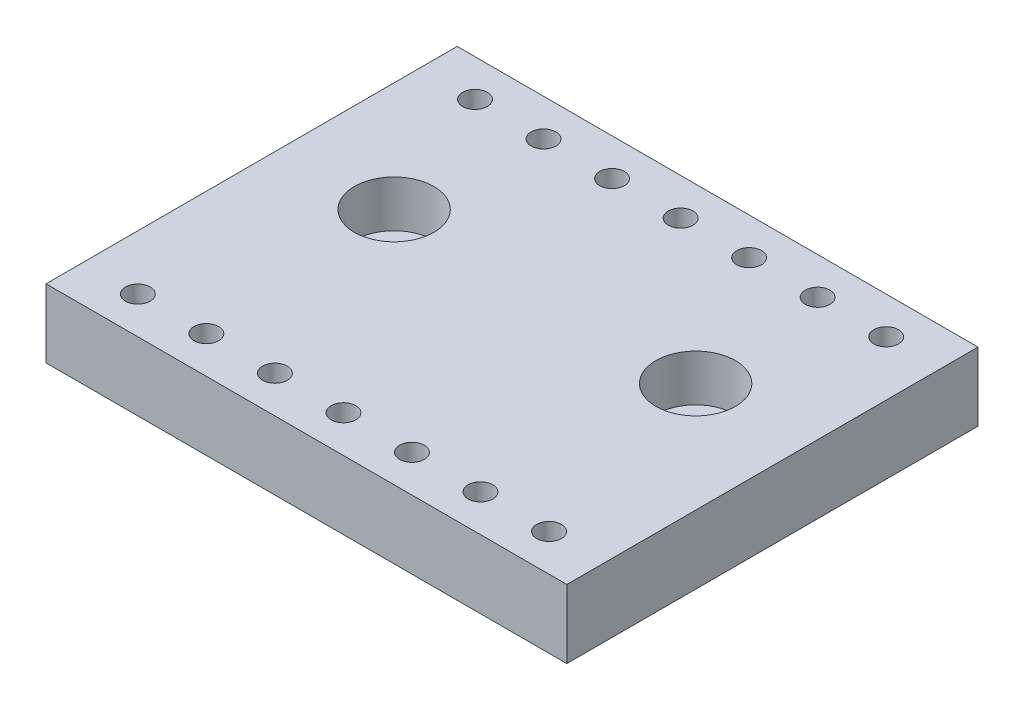
SolidWorks part; units mm, degrees
ref_plane "Front Plane" through (0, 0, 0) normal (0, 0, 1) x (1, 0, 0)
ref_plane "Top Plane" through (0, 0, 0) normal (0, 1, 0) x (1, 0, 0)
ref_plane "Right Plane" through (0, 0, 0) normal (1, 0, 0) x (0, 0, -1)
sketch "Sketch1" plane through (0, 0, 0) normal (0, 1, 0) x (1, 0, 0)
  line L1 (-24.13, 19.05) -> (24.13, 19.05)
  line L2 (-24.13, 19.05) -> (-24.13, -19.05)
  line L3 (-24.13, -19.05) -> (24.13, -19.05)
  line L4 (24.13, 19.05) -> (24.13, -19.05)
  line L5 (-24.13, 19.05) -> (24.13, -19.05) construction
  line L6 (-24.13, -19.05) -> (24.13, 19.05) construction
  point P0 (0, 0)
  dimension "D1" = 48.26
  dimension "D2" = 38.1
extrude "Boss-Extrude1" add sketch "Sketch1" against normal blind 6.35
sketch "Sketch2" plane through (0, 0, 0) normal (0, 1, 0) x (1, 0, 0)
  line L0 (-24.13, 19.05) -> (-24.13, -19.05) construction
  line L1 (-24.13, -19.05) -> (24.13, -19.05) construction
  circle A0 centre (-13.97, 3.048) radius 3.683
  dimension "D1" = 7.366
  dimension "D2" = 10.16
  dimension "D3" = 22.098
extrude "Cut-Extrude1" cut sketch "Sketch2" against normal blind 4.318
sketch "Sketch3" plane through (0, -4.318, 0) normal (0, 1, 0) x (1, 0, 0)
  circle A0 centre (-13.97, 3.048) radius 2.159
  circle A1 centre (-13.97, 3.048) radius 3.683 construction
  dimension "D1" = 4.318
  dimension "D2" = 0
extrude "Cut-Extrude2" cut sketch "Sketch3" against normal blind 4.318
sketch "Sketch4" plane through (0, 0, 0) normal (0, 1, 0) x (1, 0, 0)
  line L0 (-24.13, 19.05) -> (-24.13, -19.05) construction
  circle A0 centre (-19.05, 15.621) radius 1.143
  circle A1 centre (-19.05, -15.621) radius 1.143
  dimension "D1" = 2.286
  dimension "D2" = 2.286
  dimension "D5" = 5.08
  dimension "D3" = 31.242
  dimension "D4" = 15.621
extrude "Cut-Extrude3" cut sketch "Sketch4" against normal blind 9.398
pattern_linear "LPattern1" count 7 spacing 6.35 along (1, 0, 0) of "Cut-Extrude3"
mirror "Mirror1" about plane through (0, 0, 0) normal (1, 0, 0) of "Cut-Extrude2", "Cut-Extrude1"
